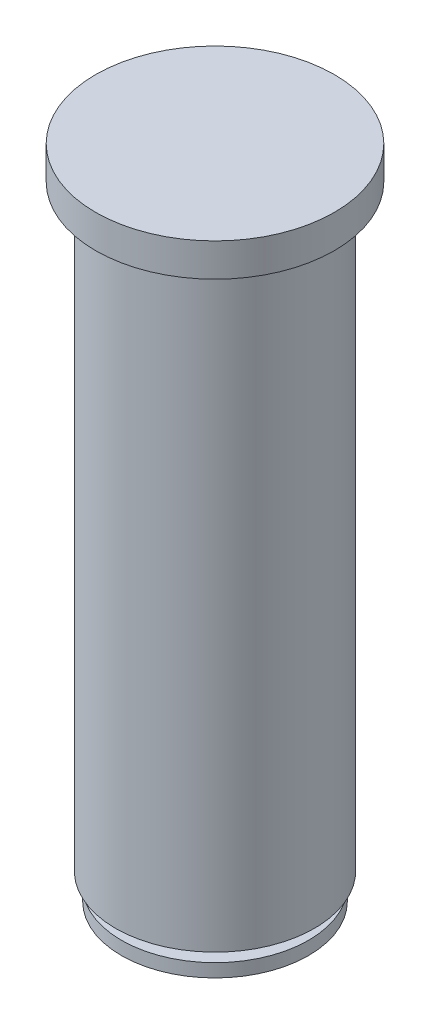
SolidWorks part; units mm, degrees
ref_plane "Front Plane" through (0, 0, 0) normal (0, 0, 1) x (1, 0, 0)
ref_plane "Top Plane" through (0, 0, 0) normal (0, 1, 0) x (1, 0, 0)
ref_plane "Right Plane" through (0, 0, 0) normal (1, 0, 0) x (0, 0, -1)
sketch "Sketch1" plane through (0, 0, 0) normal (0, 1, 0) x (1, 0, 0)
  circle A0 centre (0, 0) radius 15
  dimension "D1" = 30
extrude "Boss-Extrude1" add sketch "Sketch1" along normal blind 90
sketch "Sketch2" plane through (0, 90, 0) normal (0, 1, 0) x (1, 0, 0)
  circle A0 centre (0, 0) radius 18
  dimension "D1" = 36
extrude "Boss-Extrude2" add sketch "Sketch2" along normal blind 5
sketch "Sketch3" plane through (0, 0, 0) normal (0, -1, 0) x (1, 0, 0)
  circle A0 centre (0, 0) radius 2.5
  dimension "D1" = 5
extrude "Boss-Extrude3" add sketch "Sketch3" along normal blind 2
sketch "Sketch4" plane through (0, -2, 0) normal (0, -1, 0) x (1, 0, 0)
  circle A0 centre (0, 0) radius 14.1108
extrude "Boss-Extrude4" add sketch "Sketch4" along normal blind 2
